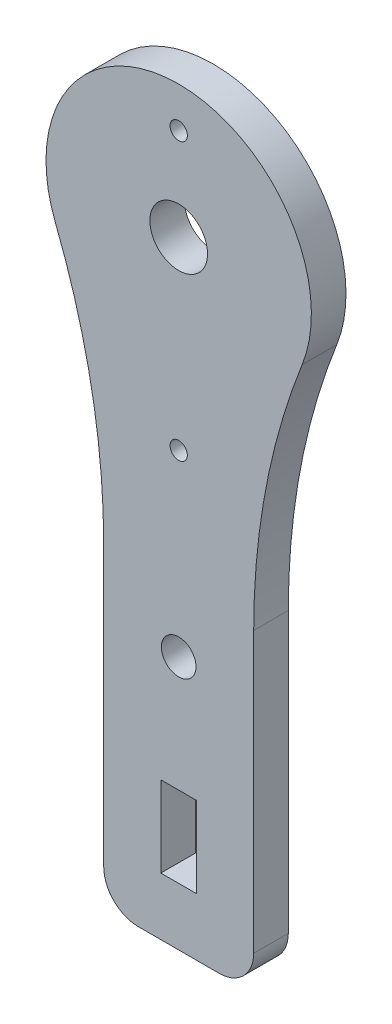
SolidWorks part; units mm, degrees
ref_plane "Alzado" through (0, 0, 0) normal (0, 0, 1) x (1, 0, 0)
ref_plane "Planta" through (0, 0, 0) normal (0, 1, 0) x (1, 0, 0)
ref_plane "Vista lateral" through (0, 0, 0) normal (1, 0, 0) x (0, 0, -1)
sketch "Croquis1" plane through (0, 0, 0) normal (0, 0, 1) x (1, 0, 0)
  line L0 (0, 0) -> (0, -26.75) construction
  line L1 (6.5, -53.5) -> (-6.5, -53.5)
  line L2 (6.5, -53.5) -> (6.5, 0)
  line L3 (6.5, 0) -> (-6.5, 0)
  line L4 (-6.5, -53.5) -> (-6.5, 0)
  line L5 (6.5, -53.5) -> (-6.5, 0) construction
  line L6 (6.5, 0) -> (-6.5, -53.5) construction
  circle A0 centre (0, 0) radius 11.5
  point P3 (0, -26.75)
  point P8 (0, 11.5)
  point P9 (0, 0)
  dimension "D2" = 23
  dimension "D1" = 65
  dimension "D3" = 13
extrude "Saliente-Extruir1" add sketch "Croquis1" along normal blind 3 contours A0 L4 L1 L2 | L4 A0 L2 L3 | L2 A0 L4 L3
sketch "Croquis2" plane through (0, 0, 3) normal (0, 0, 1) x (1, 0, 0)
  line L0 (6.5, -53.5) -> (-6.5, -53.5) construction
  line L1 (1.55, -41.5) -> (-1.55, -41.5)
  line L2 (1.55, -41.5) -> (1.55, -48.5)
  line L3 (1.55, -48.5) -> (-1.55, -48.5)
  line L4 (-1.55, -41.5) -> (-1.55, -48.5)
  line L5 (1.55, -41.5) -> (-1.55, -48.5) construction
  line L6 (1.55, -48.5) -> (-1.55, -41.5) construction
  circle A0 centre (0, 0) radius 2.5
  circle A1 centre (0, -31.5) radius 1.5
  point P6 (0, -45)
  dimension "D1" = 5
  dimension "D6" = 3
  dimension "D2" = 3.1
  dimension "D3" = 7
  dimension "D4" = 5
  dimension "D5" = 22
extrude "Cortar-Extruir1" cut sketch "Croquis2" against normal blind 3
fillet "Redondeo1" radius 60 2 edges at (6.5, -9.4868, 1.5) (-6.5, -9.4868, 1.5)
fillet "Redondeo2" radius 3 2 edges at (-6.5, -53.5, 1.5) (6.5, -53.5, 1.5)
sketch "Croquis3" plane through (0, 0, 3) normal (0, 0, 1) x (1, 0, 0)
  circle A0 centre (0, 8) radius 0.75
  circle A1 centre (0, -16) radius 0.75
  dimension "D3" = 1.5
  dimension "D1" = 8
  dimension "D2" = 24
extrude "Cortar-Extruir2" cut sketch "Croquis3" against normal blind 3
